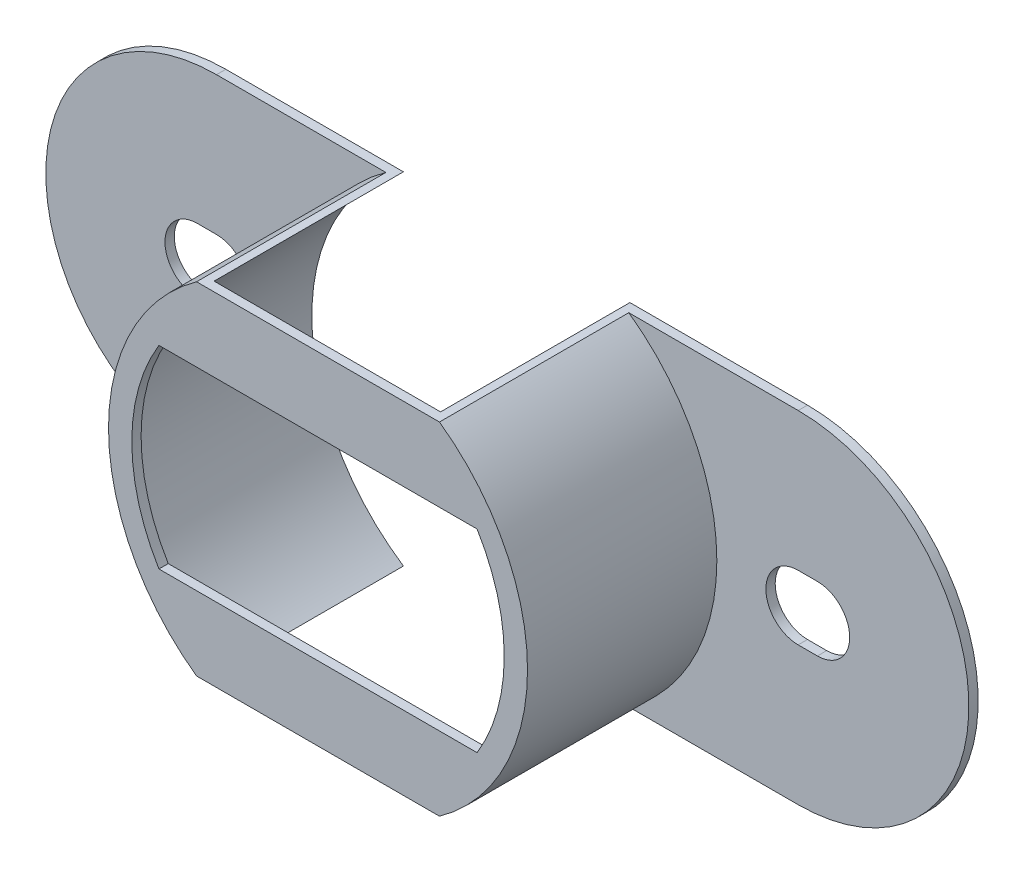
SolidWorks part; units mm, degrees
ref_plane "Front Plane" through (0, 0, 0) normal (0, 0, 1) x (1, 0, 0)
ref_plane "Top Plane" through (0, 0, 0) normal (0, 1, 0) x (1, 0, 0)
ref_plane "Right Plane" through (0, 0, 0) normal (1, 0, 0) x (0, 0, -1)
sketch "Sketch1" plane through (0, 0, 0) normal (0, 0, 1) x (1, 0, 0)
  line L1 (-11.8999, 6.985) -> (11.8999, 6.985)
  line L2 (11.8999, 1.3208) -> (12.6873, 1.3208)
  line L3 (-11.8999, -6.985) -> (11.8999, -6.985)
  line L5 (11.8999, -1.3208) -> (12.6873, -1.3208)
  line L7 (-12.6873, 1.3208) -> (-11.8999, 1.3208)
  line L9 (-12.6873, -1.3208) -> (-11.8999, -1.3208)
  arc A0 (11.8999, -6.985) -> (11.8999, 6.985) centre (11.8999, 0) ccw
  arc A1 (-11.8999, 6.985) -> (-11.8999, -6.985) centre (-11.8999, 0) ccw
  arc A2 (12.6873, -1.3208) -> (12.6873, 1.3208) centre (12.6873, 0) ccw
  arc A3 (11.8999, 1.3208) -> (11.8999, -1.3208) centre (11.8999, 0) ccw
  arc A4 (-11.8999, -1.3208) -> (-11.8999, 1.3208) centre (-11.8999, 0) ccw
  arc A5 (-12.6873, 1.3208) -> (-12.6873, -1.3208) centre (-12.6873, 0) ccw
  dimension "D3" = 6.985
  dimension "D9" = 6.985
  dimension "D2" = 6.985
  dimension "D4" = 11.8999
  dimension "D5" = 11.8999
  dimension "D6" = 0.7874
  dimension "D7" = 0.7874
  dimension "D11" = 2.6416
extrude "Extrude1" add sketch "Sketch1" along normal blind 0.381
sketch "Sketch2" plane through (0, 0, 0.381) normal (0, 0, 1) x (1, 0, 0)
  line L0 (-4.9697, -6.985) -> (4.9697, -6.985)
  line L1 (-11.8999, -6.985) -> (11.8999, -6.985) construction
  line L2 (-4.9697, 6.985) -> (4.9697, 6.985)
  line L3 (11.8999, 6.985) -> (-11.8999, 6.985) construction
  arc A0 (4.9697, -6.985) -> (4.9697, 6.985) centre (0, 0) ccw
  arc A1 (-4.9697, 6.985) -> (-4.9697, -6.985) centre (0, 0) ccw
  dimension "D1" = 17.145
extrude "Extrude2" add sketch "Sketch2" along normal blind 7.747
sketch "Sketch3" plane through (0, 0, 0) normal (0, 0, -1) x (-1, 0, 0)
  line L0 (-4.6333, 6.985) -> (4.6333, 6.985)
  line L1 (-4.6333, -6.985) -> (4.6333, -6.985)
  line L2 (11.8999, -6.985) -> (-11.8999, -6.985) construction
  line L3 (-11.8999, 6.985) -> (11.8999, 6.985) construction
  arc A0 (-4.6333, 6.985) -> (-4.6333, -6.985) centre (0, 0) ccw
  arc A1 (4.6333, -6.985) -> (4.6333, 6.985) centre (0, 0) ccw
  dimension "D1" = 16.764
extrude "Cut-Extrude1" cut sketch "Sketch3" against normal blind 7.747
sketch "Sketch4" plane through (0, 0, 8.128) normal (0, 0, 1) x (1, 0, 0)
  line L0 (-6.5087, 3.9624) -> (6.5087, 3.9624)
  line L1 (-6.5087, -3.9624) -> (6.5087, -3.9624)
  arc A0 (6.5087, -3.9624) -> (6.5087, 3.9624) centre (0, 0) ccw
  arc A1 (-6.5087, 3.9624) -> (-6.5087, -3.9624) centre (0, 0) ccw
  dimension "D1" = 15.24
  dimension "D2" = 7.9248
  dimension "D3" = 3.9624
extrude "Cut-Extrude2" cut sketch "Sketch4" against normal through all
